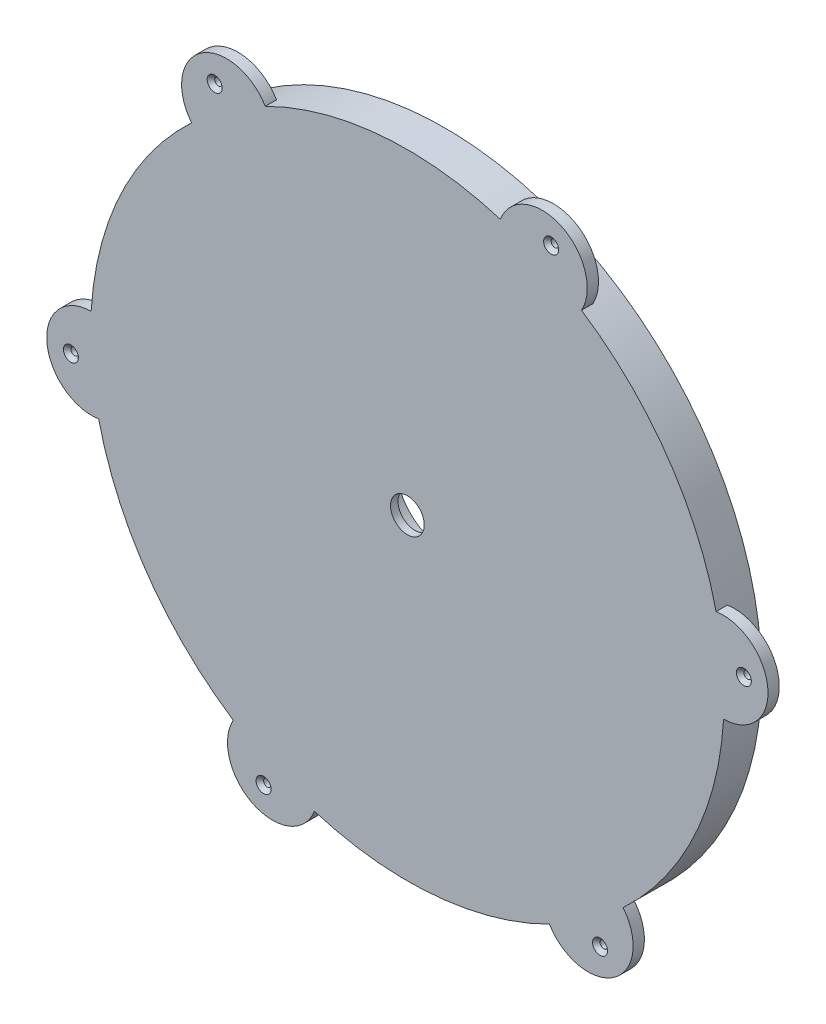
SolidWorks part; units mm, degrees
ref_plane "Front Plane" through (0, 0, 0) normal (0, 0, 1) x (1, 0, 0)
ref_plane "Top Plane" through (0, 0, 0) normal (0, 1, 0) x (1, 0, 0)
ref_plane "Right Plane" through (0, 0, 0) normal (1, 0, 0) x (0, 0, -1)
sketch "Sketch1" plane through (0, 0, 0) normal (0, 0, 1) x (1, 0, 0)
  circle A0 centre (0, 0) radius 84.5
  circle A1 centre (0, 0) radius 4.5
  dimension "D1" = 169
  dimension "D2" = 9
extrude "Boss-Extrude1" add sketch "Sketch1" along normal blind 10
sketch "Sketch2" plane through (0, 0, 0) normal (0, 0, 1) x (1, 0, 0)
  circle A0 centre (0, 0) radius 13
extrude "Cut-Extrude1" cut sketch "Sketch2" along normal blind 8
sketch "Sketch3" plane through (0, 0, 10) normal (0, 0, 1) x (1, 0, 0)
  circle A0 centre (84.2043, 7.0636) radius 12
  circle A1 centre (0, 0) radius 84.5 construction
  dimension "D1" = 24
extrude "Boss-Extrude2" add sketch "Sketch3" against normal blind 3
pattern_circular "CirPattern1" count 6 over 360 about axis through (0, 0, 0) along (0, 0, 1) of "Boss-Extrude2"
sketch "Sketch8" plane through (0, 0, 10) normal (0, 0, 1) x (1, 0, 0)
  line L0 (82.3546, 18.9202) -> (84.3557, -4.9355) construction
  line L1 (83.3552, 6.9924) -> (96.1623, 8.0667) construction
  arc A0 (84.3557, -4.9355) -> (82.3546, 18.9202) centre (84.2043, 7.0636) ccw construction
sketch "Sketch10" plane through (0, 0, 10) normal (0, 0, 1) x (1, 0, 0)
  line L0 (83.3552, 6.9924) -> (96.1623, 8.0667) construction
  point P0 (89.7587, 7.5295)
  point P1 (85.0204, 18.6507)
hole_wizard "CSK for M2 Flat Head Machine Screw1" positions "3DSketch3" profile "Sketch11" countersink size "M2" standard "ANSI Metric" end condition through all
sketch3d "3DSketch3"
  point P0 (89.7587, 7.5295, 10)
sketch "Sketch11" plane through (89.7587, 7.5295, 10) normal (1, 0, 0) x (0, -1, 0)
  line L0 (0, 0) -> (0, 10)
  line L1 (0, 10) -> (1, 10)
  line L2 (1, 10) -> (1, 1)
  line L3 (1, 1) -> (2, 0)
  line L5 (2, 0) -> (0, 0)
  line L6 (-1, 1) -> (-2, 0) construction
  line L11 (0, -6.35) -> (0, 107.95) construction
  dimension "Thru Hole Dia." = 2
  dimension "Thru Hole Depth" = 10
  dimension "Near C'Sink Dia." = 4
  dimension "Near C'Sink Angle" = 90
pattern_circular "CirPattern2" count 6 over 360 about axis through (0, 0, 0) along (0, 0, 1) of "CSK for M2 Flat Head Machine Screw1"
